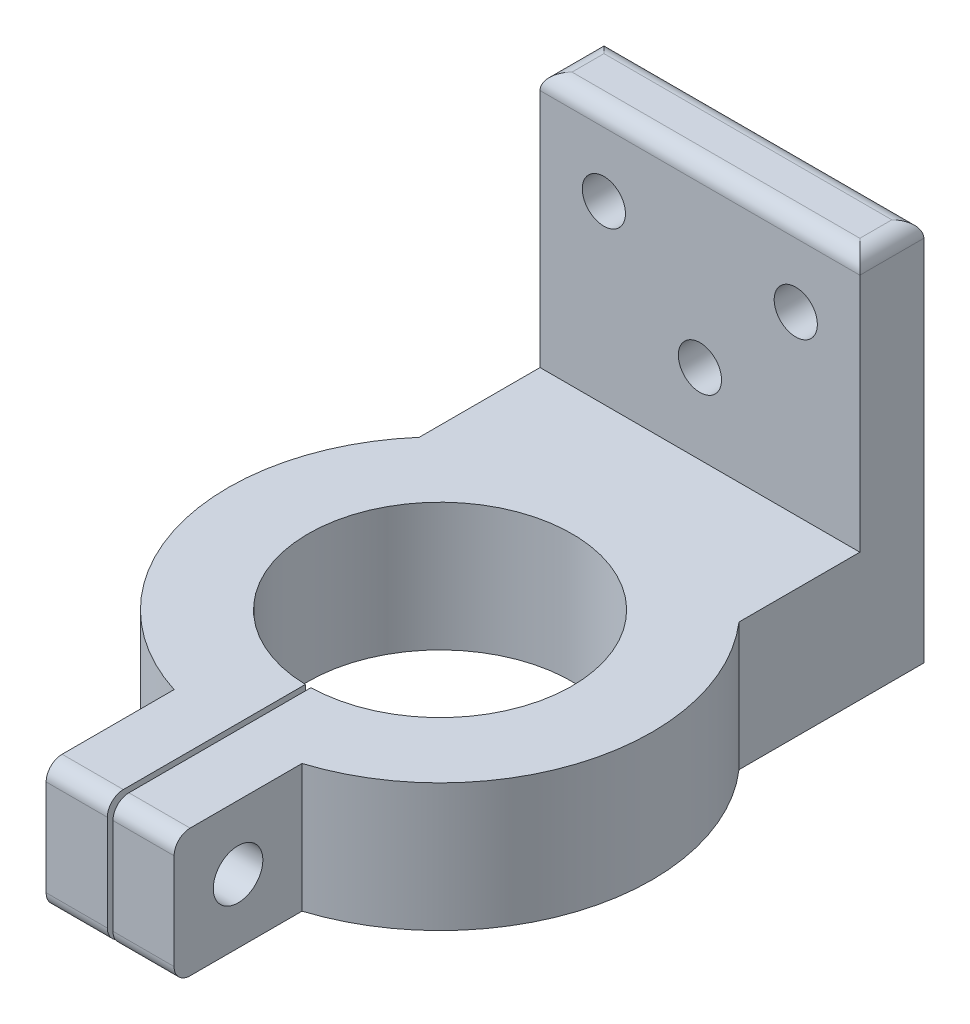
SolidWorks part; units mm, degrees
ref_plane "Front Plane" through (0, 0, 0) normal (0, 0, 1) x (1, 0, 0)
ref_plane "Top Plane" through (0, 0, 0) normal (0, 1, 0) x (1, 0, 0)
ref_plane "Right Plane" through (0, 0, 0) normal (1, 0, 0) x (0, 0, -1)
sketch "Sketch1" plane through (0, 0, 0) normal (0, 0, 1) x (1, 0, 0)
  line L1 (-10, 11) -> (10, 11)
  line L2 (-10, 11) -> (-10, -13)
  line L3 (-10, -13) -> (10, -13)
  line L4 (10, 11) -> (10, -13)
  point P4 (0, 11)
  circle B0 centre (5.992, 6) radius 1.35
  circle B1 centre (0, 0) radius 1.35
  circle B2 centre (-6.008, 6) radius 1.35
  dimension "D1" = 20
  dimension "D2" = 24
  dimension "D3" = 5
sketch_block_instance "Block1-1"
sketch_block "Block1"
extrude "Boss-Extrude1" add sketch "Sketch1" along normal blind 4
sketch "Sketch2" plane through (0, 0, 4) normal (0, 0, 1) x (1, 0, 0)
  line L0 (-10, 11) -> (-10, -13) construction
  line L1 (-10, -5) -> (10, -5)
  line L2 (-10, -5) -> (-10, -13)
  line L3 (-10, -13) -> (10, -13)
  line L4 (10, -5) -> (10, -13)
  dimension "D1" = 8
extrude "Boss-Extrude2" add sketch "Sketch2" along normal blind 8
sketch "Sketch3" plane through (0, -13, 0) normal (0, -1, 0) x (1, 0, 0)
  line L0 (-10, 12) -> (10, 12) construction
  line L3 (-4, 32.8818) -> (-4, 40.8818)
  line L4 (-4, 40.8818) -> (4, 40.8818)
  line L5 (4, 32.8818) -> (4, 40.8818)
  circle A0 centre (0, 20.25) radius 8.25
  arc A1 (-4, 32.8818) -> (4, 32.8818) centre (0, 20.25) ccw
  circle A3 centre (0, 20.25) radius 13.25 construction
  point P4 (0, 0)
  point P7 (0, 0)
  point P12 (13.25, 20.25)
  point P14 (0, 40.8818)
  dimension "D1" = 16.5
  dimension "D3" = 8
  dimension "D4" = 8
  dimension "D2" = 5
extrude "Boss-Extrude3" add sketch "Sketch3" against normal blind 8
sketch "Sketch4" plane through (0, -13, 0) normal (0, -1, 0) x (1, 0, 0)
  line L1 (-0.175, 28.4981) -> (0.175, 28.4981)
  line L2 (-0.175, 28.4981) -> (-0.175, 48.7918)
  line L3 (-0.175, 48.7918) -> (0.175, 48.7918)
  line L4 (0.175, 28.4981) -> (0.175, 48.7918)
  circle A0 centre (0, 20.25) radius 8.25 construction
  point P6 (0, 28.4981)
  dimension "D1" = 0.35
extrude "Cut-Extrude1" cut sketch "Sketch4" against normal blind 8
sketch "Sketch6" plane through (4, 0, 0) normal (1, 0, 0) x (0, 0, -1)
  line L0 (-40.8818, -5) -> (-32.8818, -13) construction
  circle A0 centre (-36.8818, -9) radius 1.55
  dimension "D1" = 3.1
extrude "Cut-Extrude2" cut sketch "Sketch6" against normal blind 8
fillet "Fillet1" radius 1 8 edges at (10, 11, 2) (0, 11, 4) (-10, 11, 2) (0, 11, 0) (-2.0875, -5, 40.8818) (-2.0875, -13, 40.8818) (2.0875, -13, 40.8818) (2.0875, -5, 40.8818)
